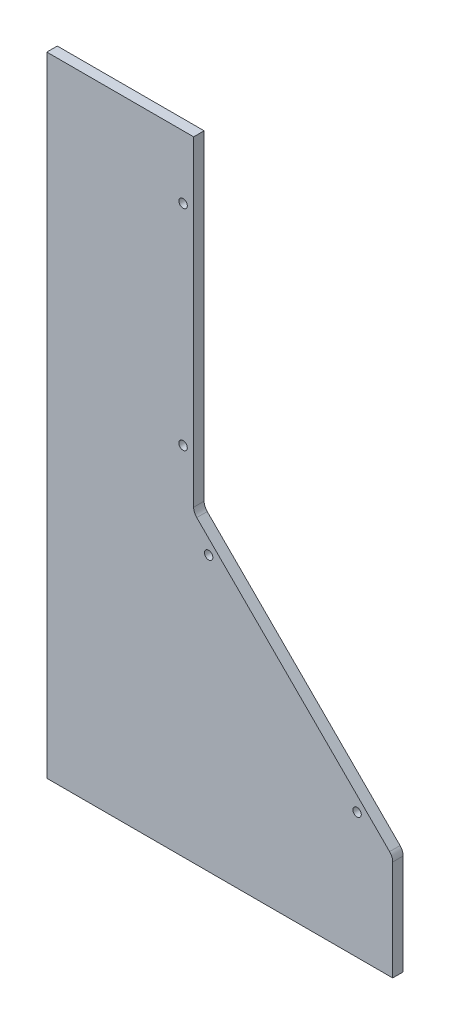
SolidWorks part; units mm, degrees
material "Pine"
ref_plane "Front Plane" through (0, 0, 0) normal (0, 0, 1) x (1, 0, 0)
ref_plane "Top Plane" through (0, 0, 0) normal (0, 1, 0) x (1, 0, 0)
ref_plane "Right Plane" through (0, 0, 0) normal (1, 0, 0) x (0, 0, -1)
sketch "Sketch1" plane through (0, 0, 0) normal (0, 0, 1) x (1, 0, 0)
  line L0 (141.4222, -15.3877) -> (141.4222, -76.2386)
  line L1 (-101.4018, 304.7614) -> (0, 304.7614)
  line L2 (-101.4018, 304.7614) -> (-101.4018, -76.2386)
  line L3 (-101.4018, -76.2386) -> (133.5482, -76.2386)
  line L5 (133.5482, -76.2386) -> (31.9482, -76.2386) construction
  line L6 (141.4222, -76.2386) -> (133.5482, -76.2386)
  line L9 (0, 108.2289) -> (20.828, 108.2289) construction
  line L11 (133.5482, -76.2386) -> (20.7722, -76.2386) construction
  line L20 (20.828, 110.4514) -> (20.828, 304.7614)
  line L21 (20.828, 304.7614) -> (0, 304.7614)
  line L24 (22.7106, 105.9386) -> (139.5395, -10.8749)
  circle A0 centre (88.0822, -57.1886) radius 3.937 construction
  circle A1 centre (88.0822, -0.0386) radius 3.937 construction
  arc A2 (141.4222, -15.3877) -> (139.5395, -10.8749) centre (135.0722, -15.3877) ccw
  arc A3 (20.828, 110.4514) -> (22.7106, 105.9386) centre (27.178, 110.4514) ccw
  point P19 (141.4222, -15.2786)
  dimension "D2" = 7.874
  dimension "D3" = 53.34
  dimension "D4" = 19.05
  dimension "D6" = 76.2
  dimension "D10" = 6.35
  dimension "D8" = 6.35
  dimension "D9" = 186.69
  dimension "D1" = 60.96
  dimension "D5" = 381
  dimension "D7" = 112.776
  dimension "D11" = 65.3637
extrude "Boss-Extrude1" add sketch "Sketch1" along normal blind 6.35
sketch "Sketch2" plane through (0, 0, 6.35) normal (0, 0, 1) x (1, 0, 0)
  line L0 (-101.4018, -76.2386) -> (-68.1278, -76.2386)
  line L1 (-101.4018, -76.2386) -> (141.4222, -76.2386) construction
  line L2 (-68.1278, -76.2386) -> (-68.1278, 304.7614)
  line L3 (20.828, 304.7614) -> (-101.4018, 304.7614) construction
  line L4 (-68.1278, 304.7614) -> (-101.4018, 304.7614)
  line L5 (-101.4018, 304.7614) -> (-101.4018, -76.2386)
  dimension "D1" = 33.274
extrude "Cut-Extrude1" cut sketch "Sketch2" against normal through all
hole_wizard "CSK for #10 Flat Head Machine Screw (100)1" positions "3DSketch1" profile "Sketch3" countersink size "#10" standard "ANSI Inch" end condition through all
sketch3d "3DSketch1"
  line L0 (141.4222, -76.2386, 0) -> (141.4222, -15.3877, 0) construction
  line L1 (-68.1278, -76.2386, 0) -> (141.4222, -76.2386, 0) construction
  point P0 (119.8322, -0.0386, 0)
  point P2 (29.9162, 89.8774, 0)
  point P4 (14.4222, 139.6614, 0)
  point P6 (14.4222, 266.6614, 0)
  dimension "D5" = 21.59
  dimension "D1" = 127
  dimension "D2" = 127
  dimension "D3" = 342.9
  dimension "D4" = 215.9
  dimension "D6" = 76.2
  dimension "D7" = 111.506
  dimension "D8" = 166.116
sketch "Sketch3" plane through (119.8322, -0.0386, 0) normal (1, 0, 0) x (0, 1, 0)
  line L0 (0, 0) -> (0, 6.35)
  line L1 (0, 6.35) -> (2.5527, 6.35)
  line L2 (2.5527, 6.35) -> (2.5527, 1.9608)
  line L3 (2.5527, 1.9608) -> (4.8895, 0)
  line L5 (4.8895, 0) -> (0, 0)
  line L6 (-2.5527, 1.9608) -> (-4.8895, 0) construction
  line L11 (0, -6.35) -> (0, 107.95) construction
  dimension "Thru Hole Dia." = 5.1054
  dimension "Thru Hole Depth" = 6.35
  dimension "Near C'Sink Dia." = 9.779
  dimension "Near C'Sink Angle" = 100
equation "\"D5@3DSketch1\"=17-16.15"
equation "\"D7@3DSketch1\"=17-12.61"
